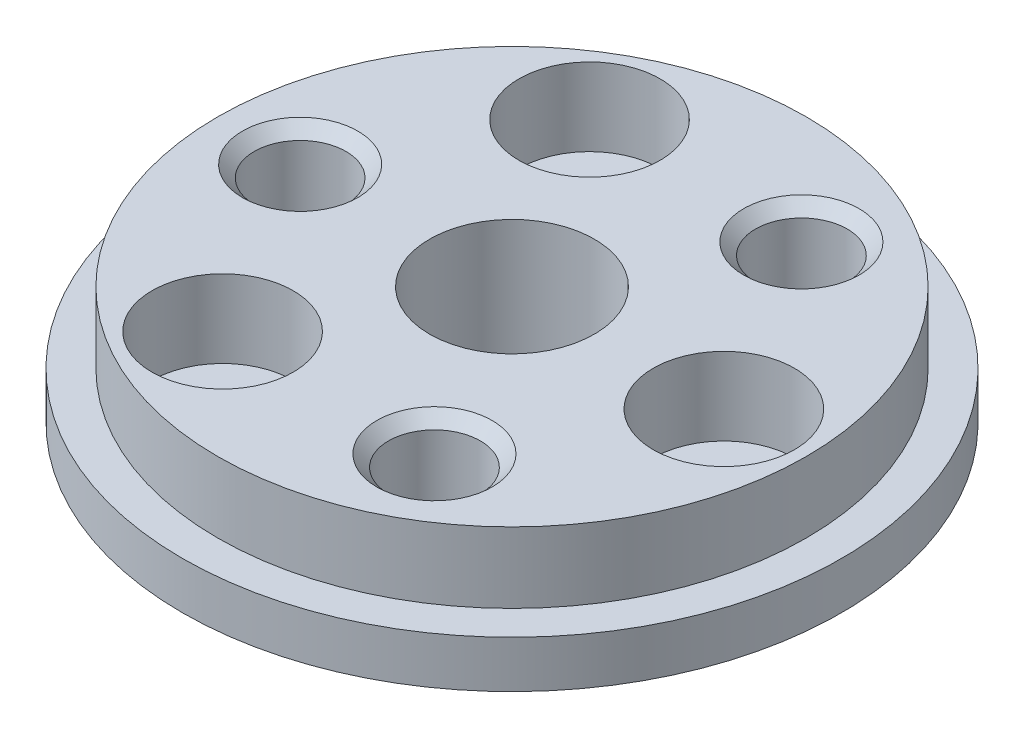
SolidWorks part; units mm, degrees
ref_plane "前视基准面" through (0, 0, 0) normal (0, 0, 1) x (1, 0, 0)
ref_plane "上视基准面" through (0, 0, 0) normal (0, 1, 0) x (1, 0, 0)
ref_plane "右视基准面" through (0, 0, 0) normal (1, 0, 0) x (0, 0, -1)
other "Configuration Table"
sketch "草图1" plane through (0, 0, 0) normal (0, 1, 0) x (1, 0, 0)
  circle A0 centre (0, 0) radius 14
  dimension "D1" = 28
extrude "凸台-拉伸1" add sketch "草图1" along normal blind 2
sketch "草图2" plane through (0, 2, 0) normal (0, 1, 0) x (1, 0, 0)
  circle A0 centre (0, 0) radius 12.5
  dimension "D1" = 25
extrude "凸台-拉伸2" add sketch "草图2" along normal blind 3
sketch "草图3" plane through (0, 5, 0) normal (0, 1, 0) x (1, 0, 0)
  circle A0 centre (9, 0) radius 1.6
  circle A1 centre (-4.5, -7.7942) radius 1.6
  circle A2 centre (-4.5, 7.7942) radius 1.6
  point P9 (0, 0)
  dimension "D1" = 3.2
  dimension "D2" = 9
  dimension "D3" = 3
extrude "切除-拉伸1" cut sketch "草图3" against normal through all
sketch "草图4" plane through (0, 5, 0) normal (0, 1, 0) x (1, 0, 0)
  circle A0 centre (9, 0) radius 3
  circle A1 centre (-4.5, 7.7942) radius 3
  circle A2 centre (-4.5, -7.7942) radius 3
  dimension "D1" = 6
extrude "切除-拉伸2" cut sketch "草图4" against normal blind 3.3
sketch "草图5" plane through (0, 5, 0) normal (0, 1, 0) x (1, 0, 0)
  line L0 (4.5, 7.7942) -> (0, 0) construction
  line L1 (0, 0) -> (9, 0) construction
  circle A0 centre (4.5, 7.7942) radius 1.95
  circle A1 centre (4.5, -7.7942) radius 1.95
  circle A2 centre (-9, 0) radius 1.95
  point P12 (0, 0)
  dimension "D2" = 3.9
  dimension "D3" = 9
  dimension "D1" = 60
  dimension "D4" = 3
extrude "切除-拉伸3" cut sketch "草图5" against normal blind 3.2
chamfer "倒角1" distance 0.5 angle 45 3 edges at (4.5, 5, -5.8442) (-9, 5, 1.95) (4.5, 5, 9.7442)
sketch "草图6" plane through (0, 5, 0) normal (0, 1, 0) x (1, 0, 0)
  circle A0 centre (0, 0) radius 3.5
  dimension "D1" = 7
extrude "切除-拉伸4" cut sketch "草图6" against normal through all
